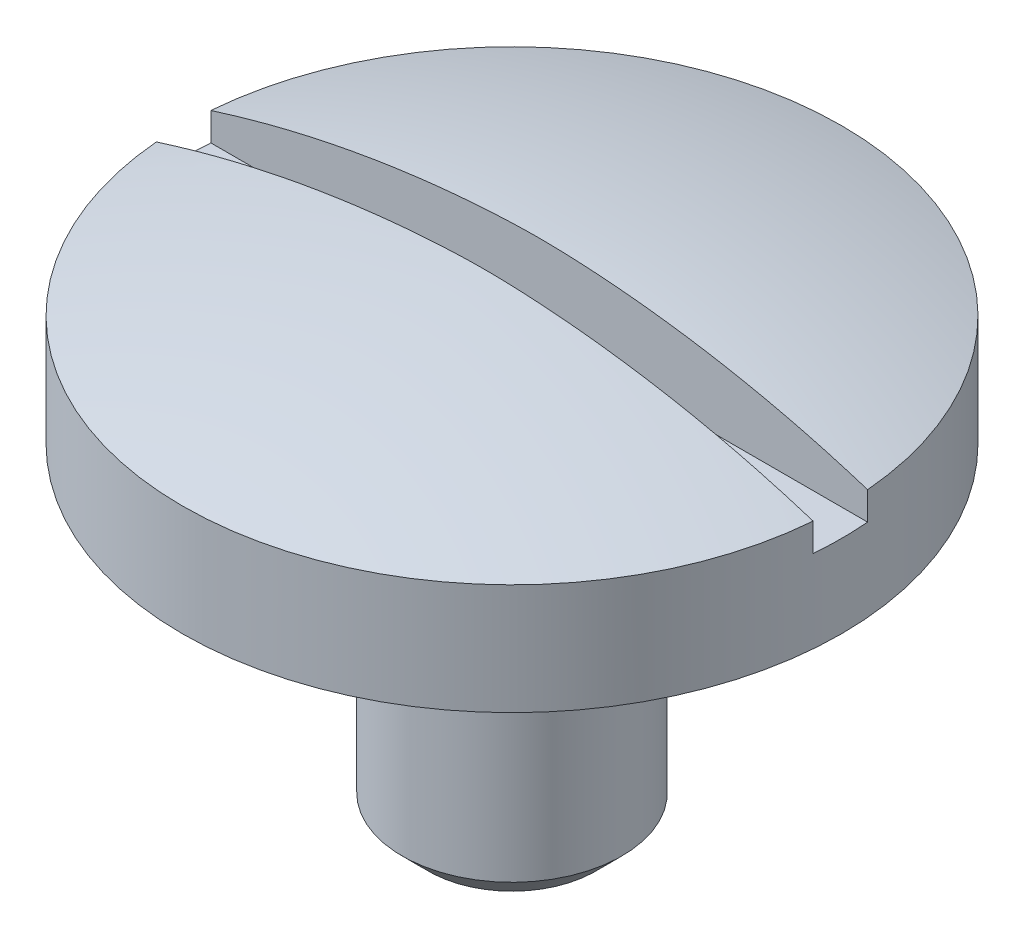
SolidWorks part; units mm, degrees
ref_plane "Front Plane" through (0, 0, 0) normal (0, 0, 1) x (1, 0, 0)
ref_plane "Top Plane" through (0, 0, 0) normal (0, 1, 0) x (1, 0, 0)
ref_plane "Right Plane" through (0, 0, 0) normal (1, 0, 0) x (0, 0, -1)
sketch "Sketch1" plane through (0, 0, 0) normal (1, 0, 0) x (0, 0, -1)
  line L0 (0, 0) -> (0, 16.0885) construction
  line L1 (0, 0) -> (3.175, 0)
  line L2 (3.175, 0) -> (3.175, 9.4996)
  line L3 (3.175, 9.4996) -> (9.525, 9.4996)
  line L4 (9.525, 9.4996) -> (9.525, 12.7)
  line L5 (0, 0) -> (0, 14.2748)
  arc A0 (9.525, 12.7) -> (0, 14.2748) centre (-0.5957, -18.9212) ccw
  dimension "D1" = 1.5748
  dimension "D2" = 4.7752
  dimension "D3" = 19.05
  dimension "D4" = 14.2748
  dimension "D5" = 6.35
revolve "Revolve1" add sketch "Sketch1" angle 360 about L0
cosmetic thread "Cosmetic Thread1" parameters "D2"=4.8387
sketch "Sketch2" plane through (0, 0, 0) normal (1, 0, 0) x (0, 0, -1)
  line L0 (0, 0) -> (0, 18.2014) construction
  line L1 (-0.7874, 11.8872) -> (0.7874, 11.8872)
  line L2 (0.7874, 11.8872) -> (0.7874, 14.2513)
  line L3 (-0.7874, 11.8872) -> (-0.7874, 14.2513)
  arc A0 (9.525, 12.7) -> (0, 14.2748) centre (-0.5957, -18.9212) ccw construction
  arc A1 (0, 14.2748) -> (-9.525, 12.7) centre (0.5957, -18.9212) ccw construction
  point P6 (0, 11.8872)
  dimension "D1" = 1.5748
  dimension "D2" = 2.3876
extrude "Cut-Extrude4" cut sketch "Sketch2" against normal through all both and the other way through all flip side to cut
chamfer "Chamfer1" distance 0.762 angle 45 1 edges at (0, 0, -3.175)
